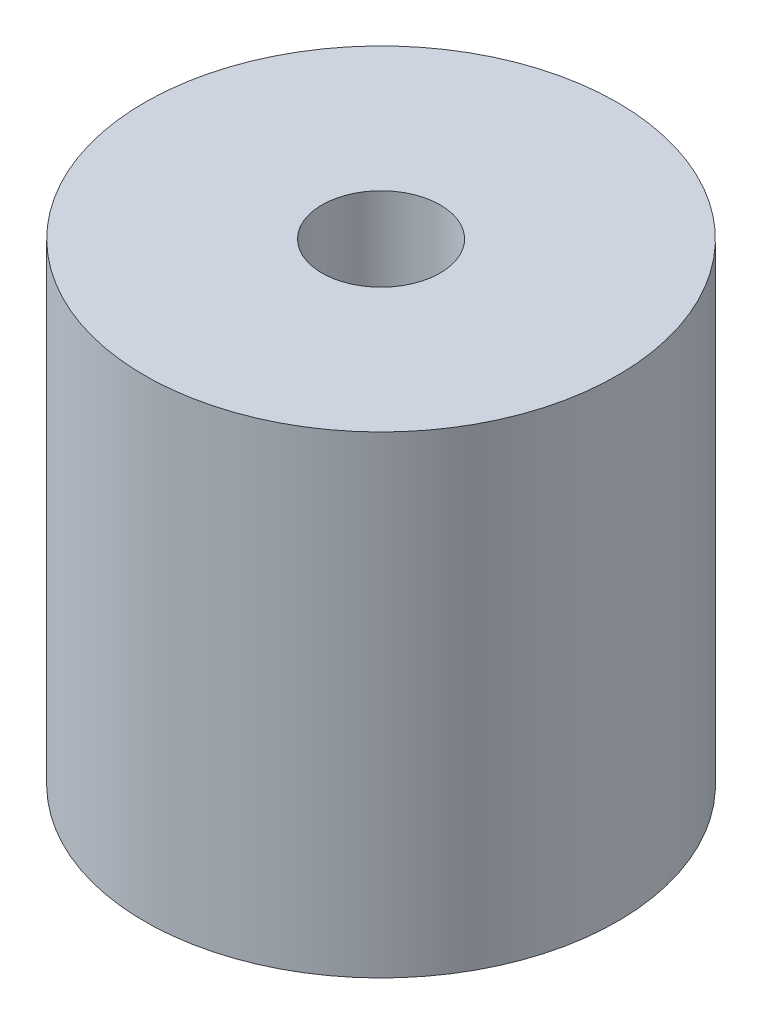
SolidWorks part; units mm, degrees
material "6061-T6 (SS)"
ref_plane "Front Plane" through (0, 0, 0) normal (0, 0, 1) x (1, 0, 0)
ref_plane "Top Plane" through (0, 0, 0) normal (0, 1, 0) x (1, 0, 0)
ref_plane "Right Plane" through (0, 0, 0) normal (1, 0, 0) x (0, 0, -1)
sketch "Sketch1" plane through (0, 0, 0) normal (0, 0, 1) x (1, 0, 0)
  line L0 (0, 0) -> (0, 20) construction
  line L1 (0, 20) -> (2.5, 20) construction
  line L2 (0, 0) -> (3, 0) construction
  line L3 (3, 0) -> (3, 10)
  line L4 (3, 10) -> (2.5, 10)
  line L5 (2.5, 10) -> (2.5, 20)
  line L6 (2.5, 20) -> (10, 20)
  line L7 (10, 20) -> (10, 0)
  line L8 (10, 0) -> (3, 0)
  dimension "D1" = 20
  dimension "D2" = 20
  dimension "D3" = 5
  dimension "D4" = 6
revolve "Revolve1" add sketch "Sketch1" angle 360 about L0
